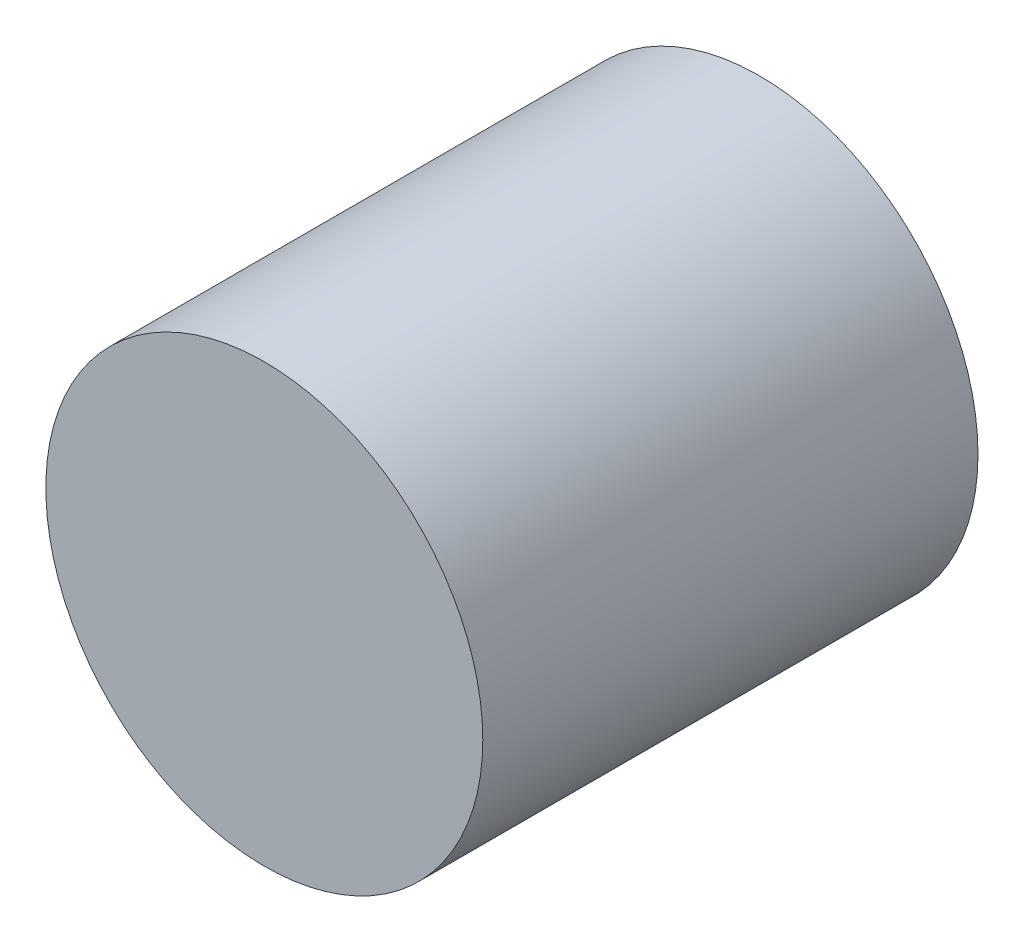
SolidWorks part; units mm, degrees
ref_plane "Front Plane" through (0, 0, 0) normal (0, 0, 1) x (1, 0, 0)
ref_plane "Top Plane" through (0, 0, 0) normal (0, 1, 0) x (1, 0, 0)
ref_plane "Right Plane" through (0, 0, 0) normal (1, 0, 0) x (0, 0, -1)
sketch "Sketch1" plane through (0, 0, 0) normal (0, 0, 1) x (1, 0, 0)
  circle A0 centre (0, 0) radius 75
  dimension "D1" = 150
extrude "Boss-Extrude1" add sketch "Sketch1" along normal blind 170
